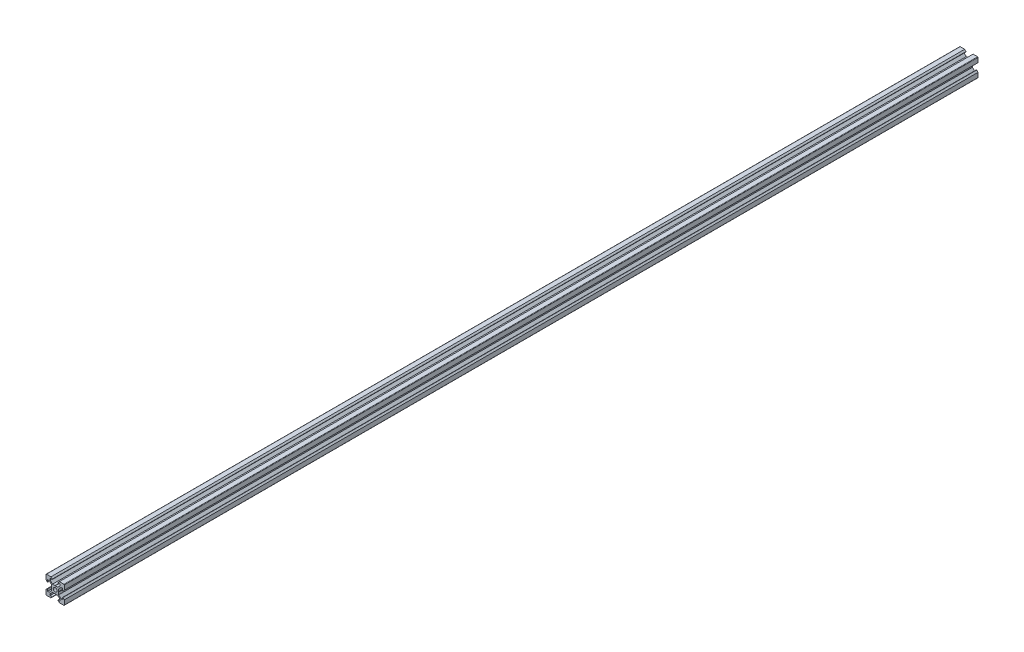
SolidWorks part; units mm, degrees
material "6061-T6 (SS)"
ref_plane "Front Plane" through (0, 0, 0) normal (0, 0, 1) x (1, 0, 0)
ref_plane "Top Plane" through (0, 0, 0) normal (0, 1, 0) x (1, 0, 0)
ref_plane "Right Plane" through (0, 0, 0) normal (1, 0, 0) x (0, 0, -1)
sketch "Sketch1" plane through (0, 0, 0) normal (0, 0, 1) x (1, 0, 0)
  line L1 (9.5, -10) -> (-9.5, -10)
  line L2 (10, -9.5) -> (10, 9.5)
  line L3 (9.5, 10) -> (-9.5, 10)
  line L4 (-10, -9.5) -> (-10, 9.5)
  line L5 (10, -10) -> (-10, 10) construction
  line L6 (10, 10) -> (-10, -10) construction
  circle A0 centre (0, 0) radius 2.1
  arc A1 (-9.5, 10) -> (-10, 9.5) centre (-9.5, 9.5) ccw
  arc A2 (10, 9.5) -> (9.5, 10) centre (9.5, 9.5) ccw
  arc A3 (9.5, -10) -> (10, -9.5) centre (9.5, -9.5) ccw
  arc A4 (-9.5, -10) -> (-10, -9.5) centre (-9.5, -9.5) cw
  point P0 (0, 0)
  line B0 (0, 0) -> (0, 10) construction
  line B1 (0, 3.69) -> (-0.21, 3.9)
  line B2 (-0.21, 3.9) -> (-2.8393, 3.9)
  line B3 (-2.8393, 3.9) -> (-5.5, 6.5607)
  line B4 (-5.5, 6.5607) -> (-5.5, 8.2)
  line B5 (-5.5, 8.2) -> (-3.125, 8.2)
  line B6 (-3.125, 8.2) -> (-3.125, 8.545)
  line B7 (-3.125, 8.545) -> (-4.58, 10)
  line B8 (-4.58, 10) -> (4.58, 10)
  line B9 (0, 0) -> (-5.9132, 5.9132) construction
  line B10 (3.125, 8.545) -> (4.58, 10)
  line B11 (3.125, 8.2) -> (3.125, 8.545)
  line B12 (5.5, 8.2) -> (3.125, 8.2)
  line B13 (5.5, 6.5607) -> (5.5, 8.2)
  line B14 (2.8393, 3.9) -> (5.5, 6.5607)
  line B15 (0.21, 3.9) -> (2.8393, 3.9)
  line B16 (0, 3.69) -> (0.21, 3.9)
  line B17 (0, 0) -> (-10, 0) construction
  line B18 (-3.69, 0) -> (-3.9, -0.21)
  line B19 (-3.9, -0.21) -> (-3.9, -2.8393)
  line B20 (-3.9, -2.8393) -> (-6.5607, -5.5)
  line B21 (-6.5607, -5.5) -> (-8.2, -5.5)
  line B22 (-8.2, -5.5) -> (-8.2, -3.125)
  line B23 (-8.2, -3.125) -> (-8.545, -3.125)
  line B24 (-8.545, -3.125) -> (-10, -4.58)
  line B25 (-10, -4.58) -> (-10, 4.58)
  line B26 (0, 0) -> (-5.9132, -5.9132) construction
  line B27 (-8.545, 3.125) -> (-10, 4.58)
  line B28 (-8.2, 3.125) -> (-8.545, 3.125)
  line B29 (-8.2, 5.5) -> (-8.2, 3.125)
  line B30 (-6.5607, 5.5) -> (-8.2, 5.5)
  line B31 (-3.9, 2.8393) -> (-6.5607, 5.5)
  line B32 (-3.9, 0.21) -> (-3.9, 2.8393)
  line B33 (-3.69, 0) -> (-3.9, 0.21)
  line B34 (0, 0) -> (0, -10) construction
  line B35 (0, -3.69) -> (0.21, -3.9)
  line B36 (0.21, -3.9) -> (2.8393, -3.9)
  line B37 (2.8393, -3.9) -> (5.5, -6.5607)
  line B38 (5.5, -6.5607) -> (5.5, -8.2)
  line B39 (5.5, -8.2) -> (3.125, -8.2)
  line B40 (3.125, -8.2) -> (3.125, -8.545)
  line B41 (3.125, -8.545) -> (4.58, -10)
  line B42 (4.58, -10) -> (-4.58, -10)
  line B43 (0, 0) -> (5.9132, -5.9132) construction
  line B44 (-3.125, -8.545) -> (-4.58, -10)
  line B45 (-3.125, -8.2) -> (-3.125, -8.545)
  line B46 (-5.5, -8.2) -> (-3.125, -8.2)
  line B47 (-5.5, -6.5607) -> (-5.5, -8.2)
  line B48 (-2.8393, -3.9) -> (-5.5, -6.5607)
  line B49 (-0.21, -3.9) -> (-2.8393, -3.9)
  line B50 (0, -3.69) -> (-0.21, -3.9)
  line B51 (0, 0) -> (10, 0) construction
  line B52 (3.69, 0) -> (3.9, 0.21)
  line B53 (3.9, 0.21) -> (3.9, 2.8393)
  line B54 (3.9, 2.8393) -> (6.5607, 5.5)
  line B55 (6.5607, 5.5) -> (8.2, 5.5)
  line B56 (8.2, 5.5) -> (8.2, 3.125)
  line B57 (8.2, 3.125) -> (8.545, 3.125)
  line B58 (8.545, 3.125) -> (10, 4.58)
  line B59 (10, 4.58) -> (10, -4.58)
  line B60 (0, 0) -> (5.9132, 5.9132) construction
  line B61 (8.545, -3.125) -> (10, -4.58)
  line B62 (8.2, -3.125) -> (8.545, -3.125)
  line B63 (8.2, -5.5) -> (8.2, -3.125)
  line B64 (6.5607, -5.5) -> (8.2, -5.5)
  line B65 (3.9, -2.8393) -> (6.5607, -5.5)
  line B66 (3.9, -0.21) -> (3.9, -2.8393)
  line B67 (3.69, 0) -> (3.9, -0.21)
  dimension "D1" = 4.2
  dimension "D3" = 0.5
  dimension "D2" = 20
sketch_block_instance "V Slot 1-4"
sketch_block "V Slot 1" parameters "D1"=10, "D2"=11, "D3"=4.3, "D4"=1.8, "D5"=0.21, "D6"=45, "D7"=9.16, "D8"=1.5, "D9"=6.25
sketch_block_instance "V Slot 1-5"
sketch_block_instance "V Slot 1-6"
sketch_block_instance "V Slot 1-7"
extrude "Boss-Extrude1" add sketch "Sketch1" along normal blind 1000 contours B67 B52 B53 B54 B55 B56 B57 B58 L2 A2 L3 B10 B11 B12 B13 B14 B15 B16 B1 B2 B3 B4 B5 B6 B7 A1 L4 B27 B28 B29 B30 B31 B32 B33 B18 B19 B20 B21 B22 B23 B24 A4 L1 B44 B45 B46 B47 B48 B49
